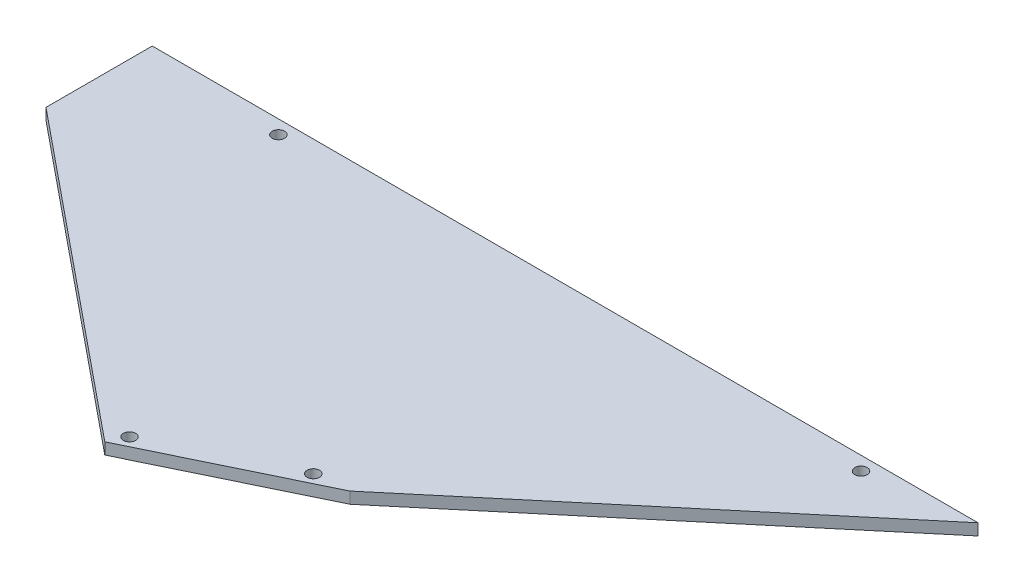
SolidWorks part; units mm, degrees
material "PC High Viscosity"
ref_plane "Front Plane" through (0, 0, 0) normal (0, 0, 1) x (1, 0, 0)
ref_plane "Top Plane" through (0, 0, 0) normal (0, 1, 0) x (1, 0, 0)
ref_plane "Right Plane" through (0, 0, 0) normal (1, 0, 0) x (0, 0, -1)
sketch "Sketch1" plane through (0, 0, 0) normal (0, 1, 0) x (1, 0, 0)
  line L5 (-189.0932, -158.668) -> (-280.5512, -202.9173)
  line L7 (0, 0) -> (-457.2, 0)
  line L10 (-189.0932, -158.668) -> (0, 0)
  line L12 (-457.2, -58.8228) -> (-457.2, 0)
  line L13 (-457.2, -58.8228) -> (-280.5512, -202.9173)
  circle A0 centre (-207.4947, -160.5169) radius 3.429
  circle A1 centre (-276.0881, -193.7038) radius 3.429
  circle A2 centre (-57.15, -7.62) radius 3.429
  circle A6 centre (-379.73, -7.62) radius 3.429
  circle A7 centre (-218.44, -7.62) radius 3.429 [skipped]
  circle A8 centre (-299.085, -7.62) radius 3.429 [skipped]
  circle A9 centre (-137.795, -7.62) radius 3.429 [skipped]
  dimension "D7" = 6.858
  dimension "D17" = 6.858
  dimension "D1" = 457.2
  dimension "D2" = 40
  dimension "D3" = 114.977
  dimension "D4" = 101.6
  dimension "D5" = 58.8228
  dimension "D6" = 76.2
  dimension "D8" = 6.35
  dimension "D9" = 6.35
  dimension "D10" = 276.0881
  dimension "D11" = 57.15
  dimension "D12" = 5
  dimension "D13" = 77.47
  dimension "D14" = 7.62
  dimension "D15" = 165.819
extrude "Boss-Extrude1" add sketch "Sketch1" along normal blind 6.35
sketch "Bend-Lines1" [suppressed] plane through (0, 0, 0) normal (0, 1, 0) x (1, 0, 0)
sketch "Bounding-Box1" [suppressed] plane through (0, 0, 0) normal (0, 1, 0) x (1, 0, 0)
